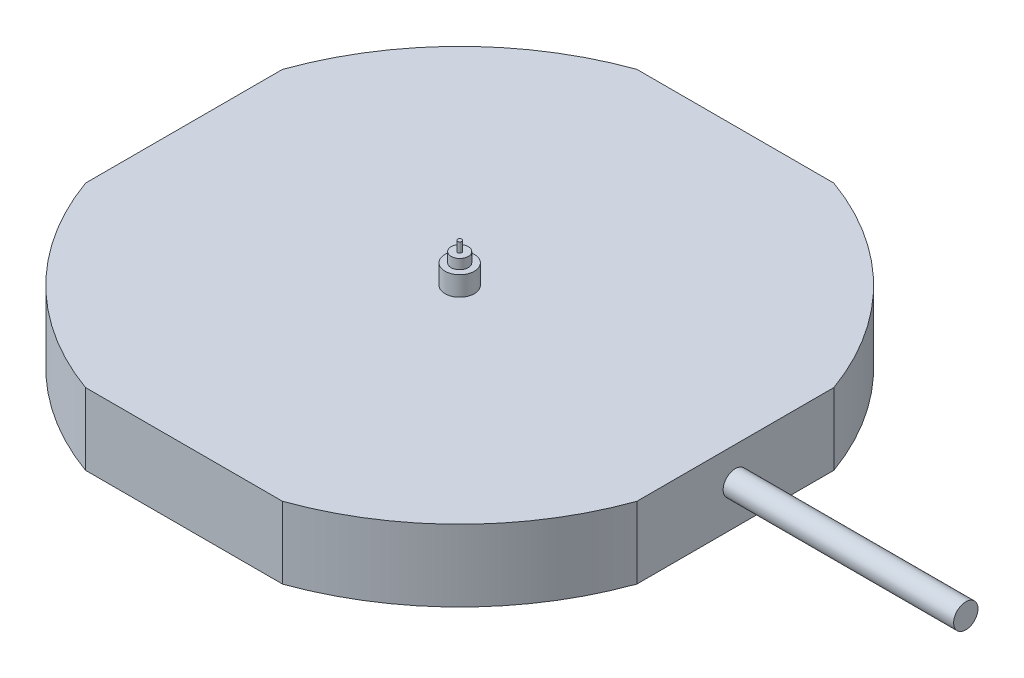
SolidWorks part; units mm, degrees
ref_plane "Front Plane" through (0, 0, 0) normal (0, 0, 1) x (1, 0, 0)
ref_plane "Top Plane" through (0, 0, 0) normal (0, 1, 0) x (1, 0, 0)
ref_plane "Right Plane" through (0, 0, 0) normal (1, 0, 0) x (0, 0, -1)
sketch "Sketch1" plane through (0, 0, 0) normal (0, 1, 0) x (1, 0, 0)
  circle A0 centre (0, 0) radius 12
extrude "Boss-Extrude1" add sketch "Sketch1" along normal blind 2.94
sketch "Sketch2" plane through (0, 0, 0) normal (0, 1, 0) x (1, 0, 0)
  line L1 (-11.3, 0) -> (-11.3, 4.7565)
  line L2 (-11.3, 4.7565) -> (-12.6284, 4.7565)
  line L4 (-11.3, 0) -> (-11.3, -4.8398)
  line L5 (-11.3, -4.8398) -> (-12.6284, -4.8398)
  line L6 (-12.6284, -4.8398) -> (-12.6284, 4.7565)
  line L7 (12.6284, -4.8398) -> (12.6284, 4.7565)
  line L8 (11.3, -4.8398) -> (12.6284, -4.8398)
  line L9 (11.3, 0) -> (11.3, -4.8398)
  line L10 (11.3, 4.7565) -> (12.6284, 4.7565)
  line L11 (11.3, 0) -> (11.3, 4.7565)
extrude "Cut-Extrude1" cut sketch "Sketch2" along normal blind 2.94
sketch "Sketch3" plane through (0, 0, 0) normal (0, 1, 0) x (1, 0, 0)
  line L1 (0, -11.3) -> (4.9982, -11.3)
  line L2 (4.9982, -11.3) -> (4.9982, -12.992)
  line L3 (0, -11.3) -> (-5.1968, -11.3)
  line L4 (-5.1968, -11.3) -> (-5.1968, -12.992)
  line L5 (-5.1968, -12.992) -> (4.9982, -12.992)
  line L6 (-5.1968, 12.992) -> (4.9982, 12.992)
  line L7 (-5.1968, 11.3) -> (-5.1968, 12.992)
  line L8 (0, 11.3) -> (-5.1968, 11.3)
  line L9 (4.9982, 11.3) -> (4.9982, 12.992)
  line L10 (0, 11.3) -> (4.9982, 11.3)
extrude "Cut-Extrude2" cut sketch "Sketch3" along normal blind 2.94
sketch "Sketch7" plane through (11.3, 0, 0) normal (1, 0, 0) x (0, 0, -1)
  circle A0 centre (0, 1.58) radius 0.5
extrude "Boss-Extrude4" add sketch "Sketch7" along normal blind 9.45
sketch "Sketch8" plane through (0, 2.94, 0) normal (0, 1, 0) x (1, 0, 0)
  circle A0 centre (0, 0) radius 0.6
extrude "Boss-Extrude5" add sketch "Sketch8" along normal blind 0.8
sketch "Sketch9" plane through (0, 3.74, 0) normal (0, 1, 0) x (1, 0, 0)
  circle A0 centre (0, 0) radius 0.35
extrude "Boss-Extrude6" add sketch "Sketch9" along normal blind 0.4
sketch "Sketch10" plane through (0, 4.14, 0) normal (0, 1, 0) x (1, 0, 0)
  circle A0 centre (0, 0) radius 0.085
extrude "Boss-Extrude7" add sketch "Sketch10" along normal blind 0.4
